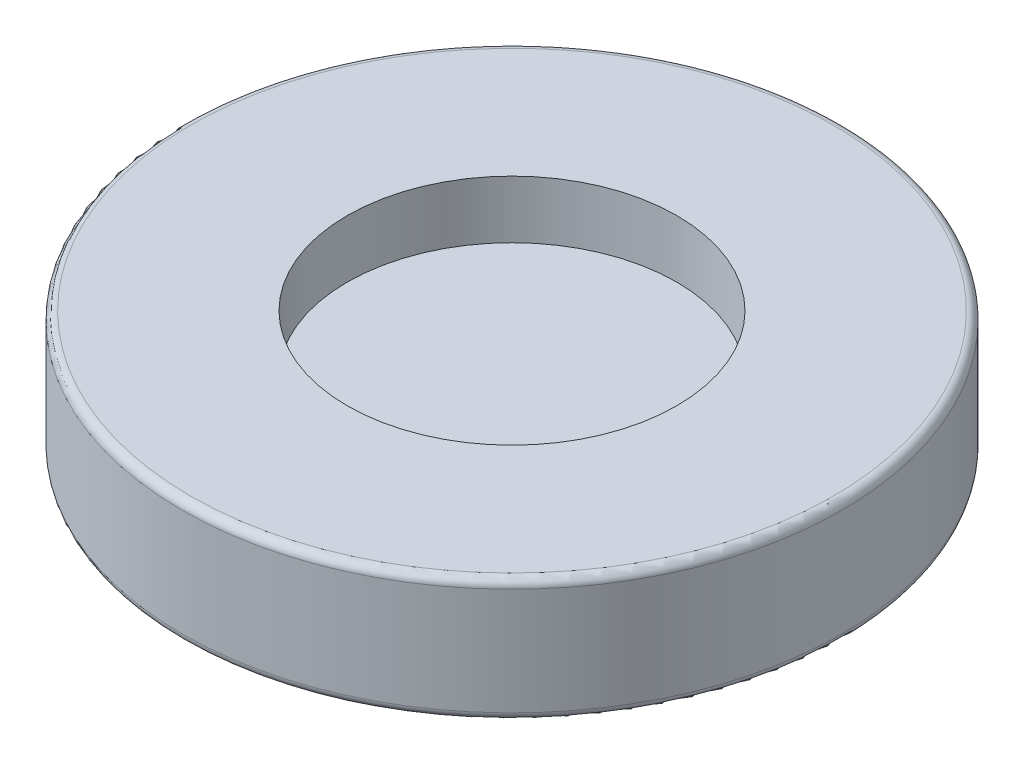
SolidWorks part; units mm, degrees
ref_plane "Front Plane" through (0, 0, 0) normal (0, 0, 1) x (1, 0, 0)
ref_plane "Top Plane" through (0, 0, 0) normal (0, 1, 0) x (1, 0, 0)
ref_plane "Right Plane" through (0, 0, 0) normal (1, 0, 0) x (0, 0, -1)
sketch "Sketch1" plane through (0, 0, 0) normal (0, 1, 0) x (1, 0, 0)
  circle A0 centre (0, 0) radius 4
  dimension "D1" = 8
extrude "Boss-Extrude1" add sketch "Sketch1" along normal blind 1.5
sketch "Sketch2" plane through (0, 1.5, 0) normal (0, 1, 0) x (1, 0, 0)
  circle A0 centre (0, 0) radius 2
  dimension "D1" = 4
extrude "Cut-Extrude1" cut sketch "Sketch2" against normal blind 0.7
fillet "Fillet2" radius 0.1 1 edges at (0, 0, 4)
fillet "Fillet3" radius 0.1 1 edges at (0, 1.5, 4)
